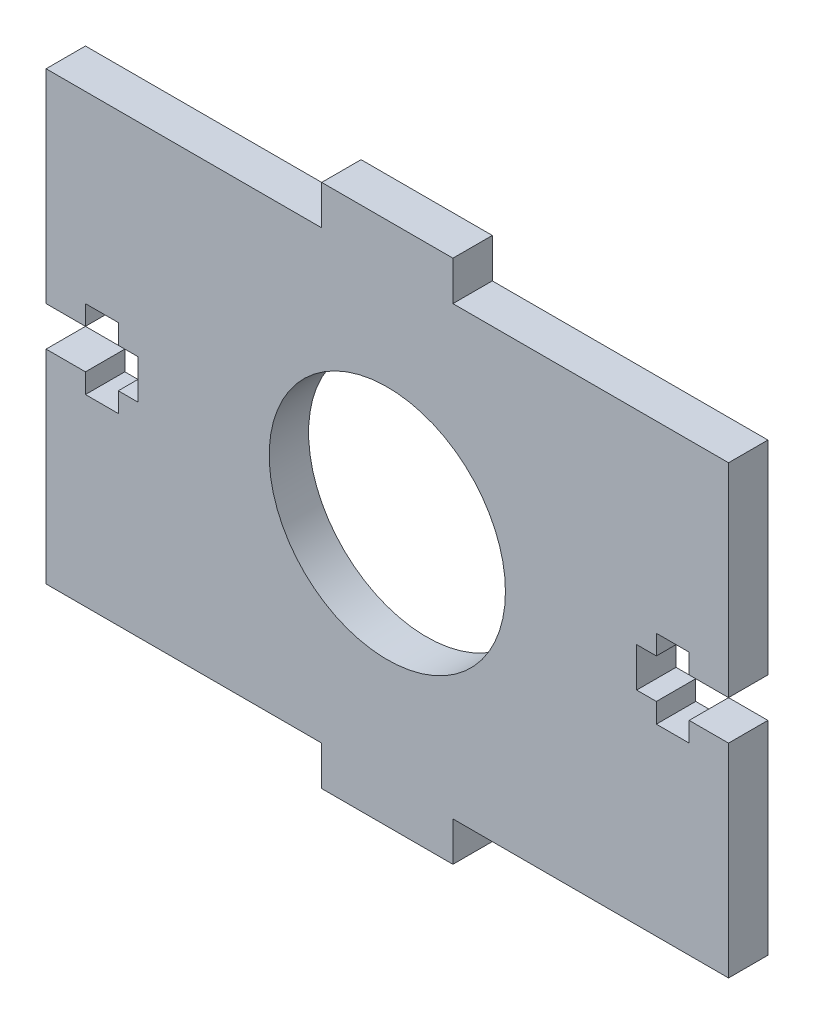
SolidWorks part; units mm, degrees
ref_plane "Front Plane" through (0, 0, 0) normal (0, 0, 1) x (1, 0, 0)
ref_plane "Top Plane" through (0, 0, 0) normal (0, 1, 0) x (1, 0, 0)
ref_plane "Right Plane" through (0, 0, 0) normal (1, 0, 0) x (0, 0, -1)
sketch "Sketch1" plane through (0, 0, 0) normal (0, 0, 1) x (1, 0, 0)
  line L0 (0, 0) -> (0, -24.1244) construction
  line L1 (-26, -17) -> (-5, -17)
  line L2 (5, 17) -> (26, 17)
  line L3 (-26, 17) -> (-5, 17)
  line L4 (0, 0) -> (-35.9377, 0) construction
  line L5 (-26, -17) -> (26, 17) construction
  line L6 (-26, 17) -> (26, -17) construction
  line L7 (-26, 1.5) -> (-23, 1.5)
  line L8 (-23, 1.5) -> (-23, 3)
  line L9 (-23, 3) -> (-20.5, 3)
  line L10 (-20.5, 3) -> (-20.5, 1.5)
  line L11 (-20.5, 1.5) -> (-19, 1.5)
  line L12 (-19, 1.5) -> (-19, -1.5)
  line L13 (-20.5, -1.5) -> (-19, -1.5)
  line L14 (-20.5, -3) -> (-20.5, -1.5)
  line L15 (-23, -3) -> (-20.5, -3)
  line L16 (-23, -1.5) -> (-23, -3)
  line L17 (-26, -1.5) -> (-23, -1.5)
  line L18 (-26, -1.5) -> (-26, -17)
  line L19 (26, -1.5) -> (23, -1.5)
  line L20 (5, -17) -> (26, -17)
  line L21 (5, 17) -> (5, 20)
  line L22 (5, 20) -> (-5, 20)
  line L23 (-5, 17) -> (-5, 20)
  line L24 (5, 17) -> (-5, 20) construction
  line L25 (5, 20) -> (-5, 17) construction
  line L27 (5, -17) -> (5, -20)
  line L28 (5, -20) -> (-5, -20)
  line L29 (-5, -17) -> (-5, -20)
  line L30 (5, -17) -> (-5, -20) construction
  line L31 (5, -20) -> (-5, -17) construction
  line L32 (23, -1.5) -> (23, -3)
  line L33 (23, -3) -> (20.5, -3)
  line L34 (26, 17) -> (26, 1.5)
  line L35 (20.5, -3) -> (20.5, -1.5)
  line L36 (-26, 17) -> (-26, 1.5)
  line L37 (26, 17) -> (-26, -17) construction
  line L38 (26, -17) -> (-26, 17) construction
  line L39 (20.5, -1.5) -> (19, -1.5)
  line L40 (19, 1.5) -> (19, -1.5)
  line L41 (20.5, 1.5) -> (19, 1.5)
  line L42 (20.5, 3) -> (20.5, 1.5)
  line L43 (23, 3) -> (20.5, 3)
  line L44 (23, 1.5) -> (23, 3)
  line L45 (26, 1.5) -> (23, 1.5)
  line L46 (26, -1.5) -> (26, -17)
  circle A0 centre (0, 0) radius 9
  point P0 (0, 0)
  point P9 (-19, 0)
  point P22 (0, 18.5)
  point P27 (0, -18.5)
  point P28 (-19, 0)
  point P45 (19, 0)
  dimension "D9" = 3
  dimension "D12" = 18
  dimension "D1" = 34
  dimension "D2" = 52
  dimension "D3" = 3
  dimension "D4" = 1.5
  dimension "D5" = 3
  dimension "D6" = 10
  dimension "D7" = 3
  dimension "D8" = 10
  dimension "D10" = 7
  dimension "D11" = 2.5
extrude "Boss-Extrude1" add sketch "Sketch1" along normal blind 3
